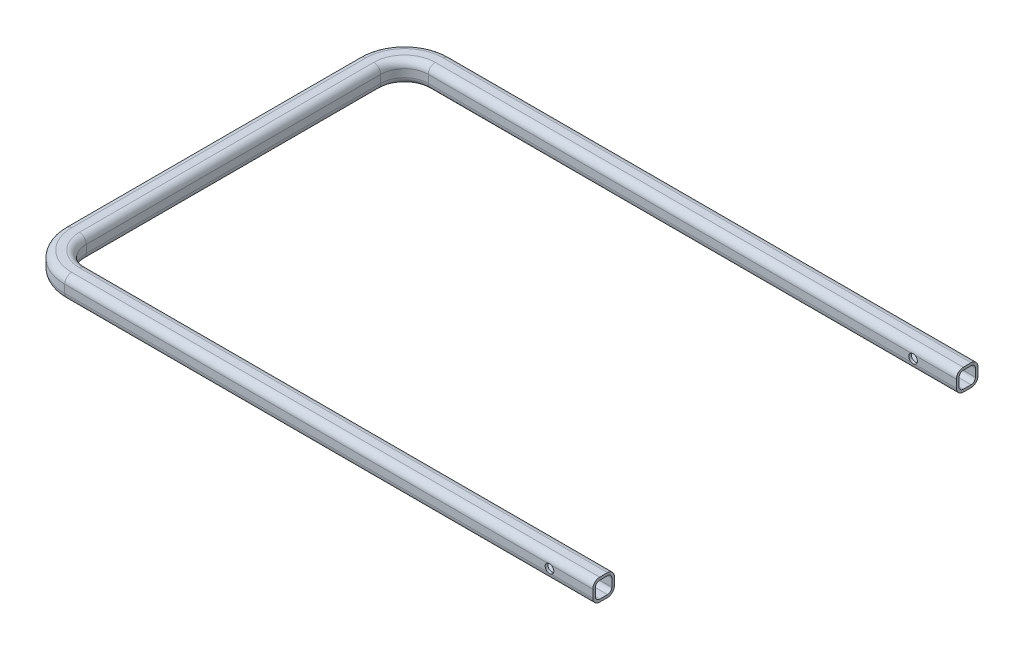
SolidWorks part; units mm, degrees
material "5052-H38, Rod (SS)"
ref_plane "Front Plane" through (0, 0, 0) normal (0, 0, 1) x (1, 0, 0)
ref_plane "Top Plane" through (0, 0, 0) normal (0, 1, 0) x (1, 0, 0)
ref_plane "Right Plane" through (0, 0, 0) normal (1, 0, 0) x (0, 0, -1)
sketch "Sketch1" plane through (0, 0, 0) normal (0, 1, 0) x (1, 0, 0)
  line L0 (0, 0) -> (-610, 0)
  line L1 (-650, 40) -> (-650, 380)
  line L2 (-610, 420) -> (0, 420)
  line L3 (-50, 0) -> (-50, 420) construction
  line L4 (-650, 210) -> (-657.5631, 210) construction
  arc A0 (-610, 0) -> (-650, 40) centre (-610, 40) cw
  arc A1 (-610, 420) -> (-650, 380) centre (-610, 380) ccw
  point P7 (-650, 0)
  point P10 (-650, 420)
  dimension "D3" = 40
  dimension "D1" = 650
  dimension "D2" = 420
  dimension "D4" = 50
sketch "Sketch2" plane through (0, 0, 0) normal (1, 0, 0) x (0, 0, -1)
  line L1 (-4.5, -9.5) -> (4.5, -9.5)
  line L2 (-9.5, -4.5) -> (-9.5, 4.5)
  line L3 (-4.5, 9.5) -> (4.5, 9.5)
  line L4 (9.5, -4.5) -> (9.5, 4.5)
  line L5 (-9.5, -9.5) -> (9.5, 9.5) construction
  line L6 (-9.5, 9.5) -> (9.5, -9.5) construction
  arc A0 (-4.5, 9.5) -> (-9.5, 4.5) centre (-4.5, 4.5) ccw
  arc A1 (-9.5, -4.5) -> (-4.5, -9.5) centre (-4.5, -4.5) ccw
  arc A2 (4.5, -9.5) -> (9.5, -4.5) centre (4.5, -4.5) ccw
  arc A3 (9.5, 4.5) -> (4.5, 9.5) centre (4.5, 4.5) ccw
  point P0 (0, 0)
  dimension "D3" = 5
  dimension "D1" = 19
  dimension "D2" = 19
sweep "Sweep-Thin1" add profiles "Sketch2" path "Sketch1" parameters "D1"=3
sketch "Sketch3" plane through (0, 0, 0) normal (0, 0, 1) x (1, 0, 0)
  line L0 (0, 0) -> (-610, 0) construction
  circle A0 centre (-50, 0) radius 5
  dimension "D1" = 50
extrude "Cut-Extrude1" cut sketch "Sketch3" against normal through all and the other way through all
sketch "Sketch4" plane through (0, 0, -12.5) normal (0, 0, -1) x (-1, 0, 0)
  line L0 (0, 0) -> (45, 0) construction
  line L1 (0, -4.5) -> (0, 4.5) construction
  arc A0 (47.8206, 4.5) -> (47.8206, -4.5) centre (50, 0) ccw construction
ref_plane "Plane1" through (-650, 0, 0) normal (1, 0, 0) x (0, 0, -1)
sketch "Sketch5" plane through (-650, 0, 0) normal (1, 0, 0) x (0, 0, -1)
  line L0 (380, 0) -> (38.7593, 0) construction
  line L1 (209.3797, 0) -> (281.8797, 0) construction
  line L3 (209.3797, 0) -> (136.8797, 0) construction
  line L4 (281.8797, 0) -> (281.8797, -50) construction
  line L5 (136.8797, 0) -> (136.8797, -50) construction
  dimension "D1" = 72.5
  dimension "D2" = 72.5
ref_plane "Plane2" through (0, 0, -210) normal (0, 0, -1) x (-1, 0, 0)
